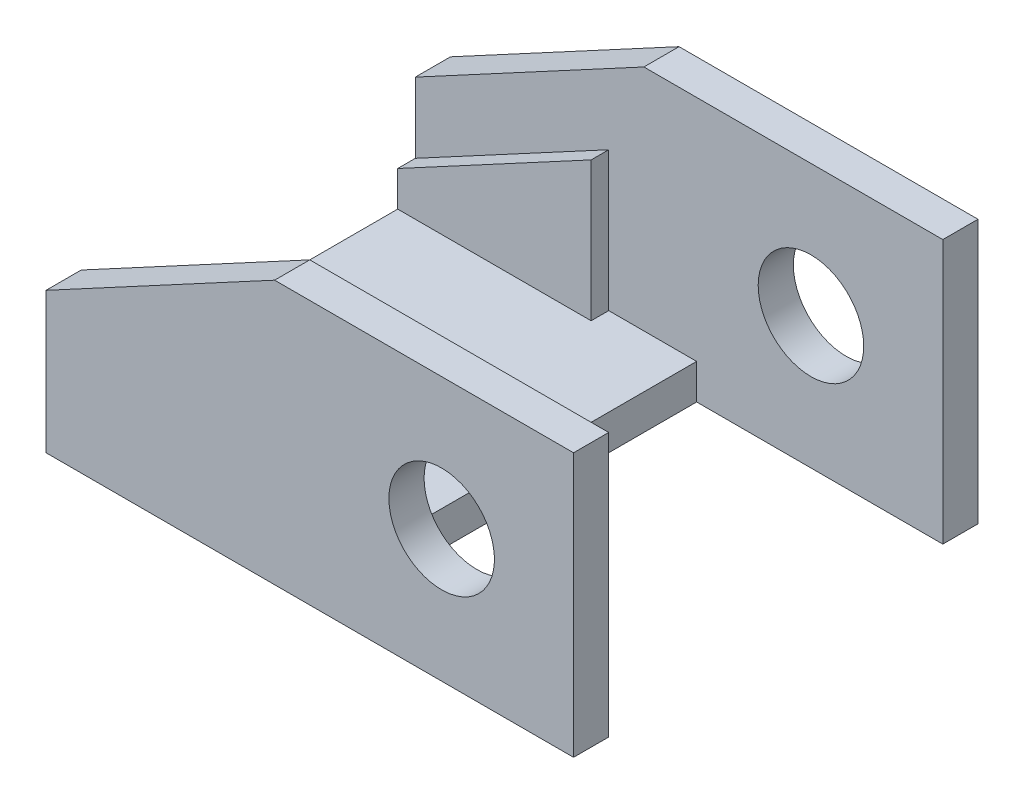
SolidWorks part; units mm, degrees
ref_plane "Plan de face" through (0, 0, 0) normal (0, 0, 1) x (1, 0, 0)
ref_plane "Plan de dessus" through (0, 0, 0) normal (0, 1, 0) x (1, 0, 0)
ref_plane "Plan de droite" through (0, 0, 0) normal (1, 0, 0) x (0, 0, -1)
sketch "Esquisse2" plane through (0, 0, 0) normal (0, 1, 0) x (1, 0, 0)
  line L0 (0, 0) -> (-11.3325, 0) construction
  line L1 (-8, 9.5) -> (8, 9.5)
  line L2 (-8, 9.5) -> (-8, 0)
  line L3 (-8, 0) -> (8, 0)
  line L4 (8, 9.5) -> (8, 0)
  line L5 (-8, 9.5) -> (8, 0) construction
  line L6 (-8, 0) -> (8, 9.5) construction
  point P0 (0, 4.75)
  dimension "D1" = 19
  dimension "D2" = 16
extrude "Boss.-Extru.1" add sketch "Esquisse2" along normal blind 2
sketch "Esquisse5" plane through (0, 0, 0) normal (0, -1, 0) x (1, 0, 0)
  line L0 (8, -9.5) -> (-8, -9.5) construction
  line L1 (8, -9.5) -> (-8, -9.5)
  line L2 (8, -9.5) -> (8, -11.5)
  line L3 (8, -11.5) -> (-8, -11.5)
  line L4 (-8, -9.5) -> (-8, -11.5)
  line L5 (8, -9.5) -> (-8, -11.5) construction
  line L6 (8, -11.5) -> (-8, -9.5) construction
  line L7 (8, 0) -> (8, -9.5) construction
  line L8 (-8, -9.5) -> (-8, 0) construction
  point P0 (0, -10.5)
  dimension "D1" = 2
extrude "Boss.-Extru.2" add sketch "Esquisse5" against normal blind 15
sketch "Esquisse6" plane through (0, 0, -11.5) normal (0, 0, -1) x (-1, 0, 0)
  line L0 (-5, 15) -> (8, 8)
  line L1 (8, 15) -> (-8, 15) construction
  line L2 (8, 15) -> (8, 0) construction
  line L3 (-8, 15) -> (-8, 0) construction
  dimension "D1" = 8
  dimension "D2" = 3
extrude "Enlèv. mat.-Extru.1" cut sketch "Esquisse6" against normal through all and the other way through all
sketch "Esquisse7" plane through (8, 0, 0) normal (1, 0, 0) x (0, 0, -1)
  line L0 (11.5, 15) -> (9.5, 15) construction
  line L1 (9.5, 15) -> (11.5, 15)
  line L2 (9.5, 15) -> (9.5, 0)
  line L3 (9.5, 0) -> (11.5, 0)
  line L4 (11.5, 15) -> (11.5, 0)
  line L5 (9.5, 15) -> (11.5, 0) construction
  line L6 (9.5, 0) -> (11.5, 15) construction
  line L7 (9.5, 15) -> (9.5, 2) construction
  point P0 (10.5, 7.5)
extrude "Boss.-Extru.3" add sketch "Esquisse7" along normal blind 14
sketch "Esquisse8" plane through (0, 0, -9.5) normal (0, 0, 1) x (1, 0, 0)
  line L0 (-8, 2) -> (-8, 4)
  line L1 (-8, 8) -> (-8, 2) construction
  line L2 (-8, 4) -> (3, 9.9231)
  line L3 (3, 9.9231) -> (3, 2)
  line L4 (8, 2) -> (-8, 2) construction
  line L5 (3, 2) -> (-8, 2)
  line L6 (5, 15) -> (-8, 8) construction
  dimension "D1" = 2
  dimension "D2" = 5
extrude "Boss.-Extru.4" add sketch "Esquisse8" along normal blind 1
sketch "Esquisse9" plane through (0, 0, -11.5) normal (0, 0, -1) x (-1, 0, 0)
  line L0 (-22, 0) -> (-22, 15) construction
  line L1 (-14.5, 15) -> (-14.5, 0) construction
  line L3 (8, 0) -> (-22, 0) construction
  circle A0 centre (-14.5, 7.5) radius 3
  dimension "D2" = 6
  dimension "D1" = 7.5
extrude "Enlèv. mat.-Extru.2" cut sketch "Esquisse9" against normal up to next
mirror "Symétrie1" about plane through (-8, 2, 0) normal (0, 0, -1) of bodies 106
sketch "Esquisse11" plane through (0, 2, 0) normal (0, 1, 0) x (1, 0, 0)
  line L0 (-8, 0) -> (8, 0) construction
  line L1 (-8, 8.5) -> (-8, -8.5) construction
  line L2 (8, -9.5) -> (8, 9.5) construction
  circle A0 centre (-4, 0) radius 1.5
  circle A1 centre (4, 0) radius 1.5
  dimension "D2" = 3
  dimension "D1" = 4
  dimension "D3" = 4
extrude "Enlèv. mat.-Extru.3" cut sketch "Esquisse11" against normal up to next
chamfer "Chanfrein1" distance 1 angle 60 2 edges at (-4, 2, 1.5) (4, 2, 1.5)
